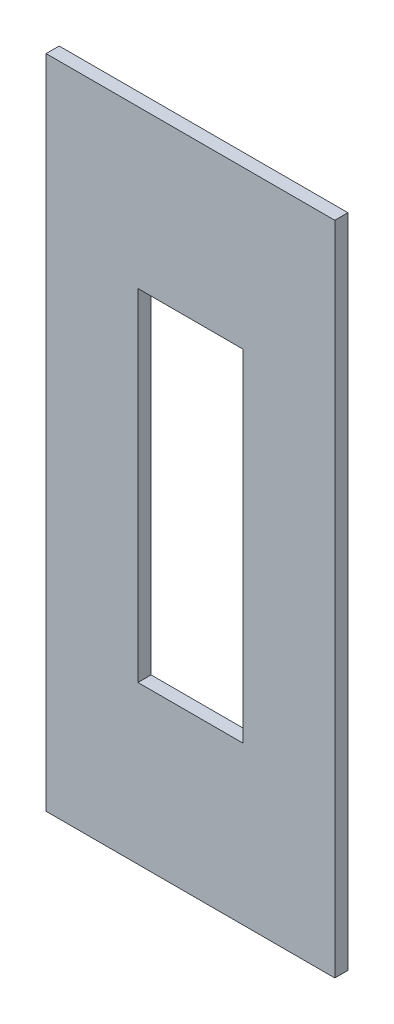
SolidWorks part; units mm, degrees
material "Никель"
ref_plane "Спереди" through (0, 0, 0) normal (0, 0, 1) x (1, 0, 0)
ref_plane "Сверху" through (0, 0, 0) normal (0, 1, 0) x (1, 0, 0)
ref_plane "Справа" through (0, 0, 0) normal (1, 0, 0) x (0, 0, -1)
sketch "Эскиз1" plane through (0, 0, 0) normal (0, 0, 1) x (1, 0, 0)
  line L0 (-2, 6.5) -> (2, -6.5) construction
  line L1 (-5.5, 12.5) -> (5.5, 12.5)
  line L2 (-5.5, 12.5) -> (-5.5, -12.5)
  line L3 (-5.5, -12.5) -> (5.5, -12.5)
  line L4 (5.5, 12.5) -> (5.5, -12.5)
  line L5 (-2, 6.5) -> (2, 6.5)
  line L6 (-2, 6.5) -> (-2, -6.5)
  line L7 (-2, -6.5) -> (2, -6.5)
  line L8 (2, 6.5) -> (2, -6.5)
  line L9 (2, 6.5) -> (-2, -6.5) construction
  line L10 (5.5, 12.5) -> (-5.5, -12.5) construction
  line L11 (5.5, -12.5) -> (-5.5, 12.5) construction
  dimension "D1" = 4
  dimension "D2" = 13
  dimension "D3" = 11
  dimension "D4" = 25
extrude "Вытянуть1" add sketch "Эскиз1" along normal blind 0.5 contours L4 L1 L2 L3 L5 L8 L7 L6
sketch3d "Трехмерный эскиз1"
  point P0 (0, 0, 0)
